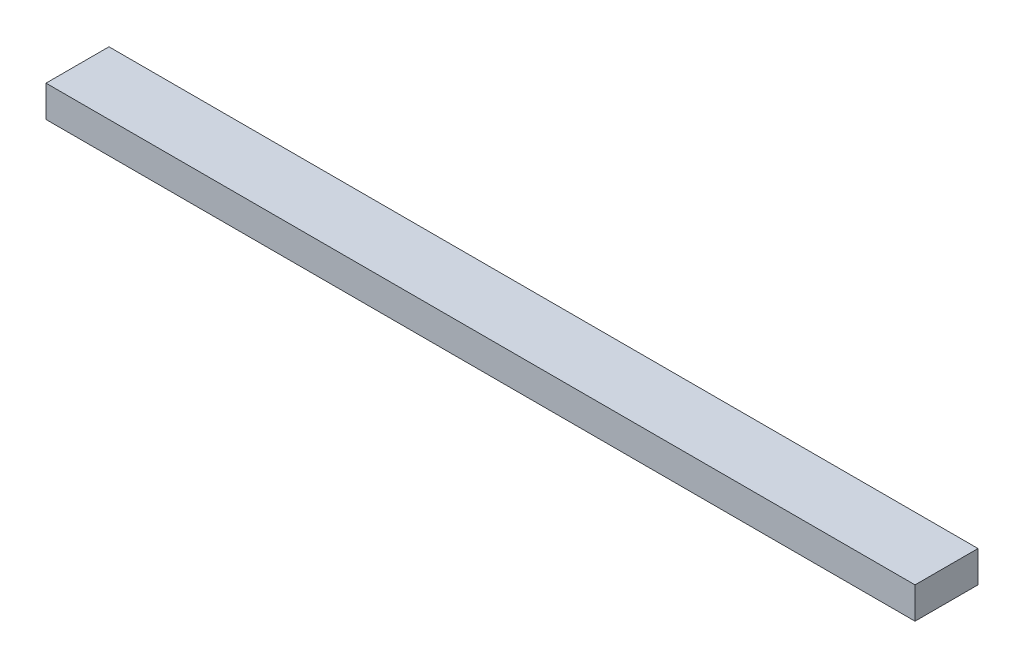
SolidWorks part; units mm, degrees
material "AISI 1010 Steel, hot rolled bar"
ref_plane "Front Plane" through (0, 0, 0) normal (0, 0, 1) x (1, 0, 0)
ref_plane "Top Plane" through (0, 0, 0) normal (0, 1, 0) x (1, 0, 0)
ref_plane "Right Plane" through (0, 0, 0) normal (1, 0, 0) x (0, 0, -1)
sketch "Sketch1" plane through (0, 0, 0) normal (0, 1, 0) x (1, 0, 0)
  line L1 (-87.63, -6.35) -> (87.63, -6.35)
  line L2 (-87.63, -6.35) -> (-87.63, 6.35)
  line L3 (-87.63, 6.35) -> (87.63, 6.35)
  line L4 (87.63, -6.35) -> (87.63, 6.35)
  line L5 (-87.63, -6.35) -> (87.63, 6.35) construction
  line L6 (-87.63, 6.35) -> (87.63, -6.35) construction
  point P0 (0, 0)
  dimension "D1" = 175.26
  dimension "D2" = 12.7
extrude "Boss-Extrude1" add sketch "Sketch1" along normal blind 6.35
